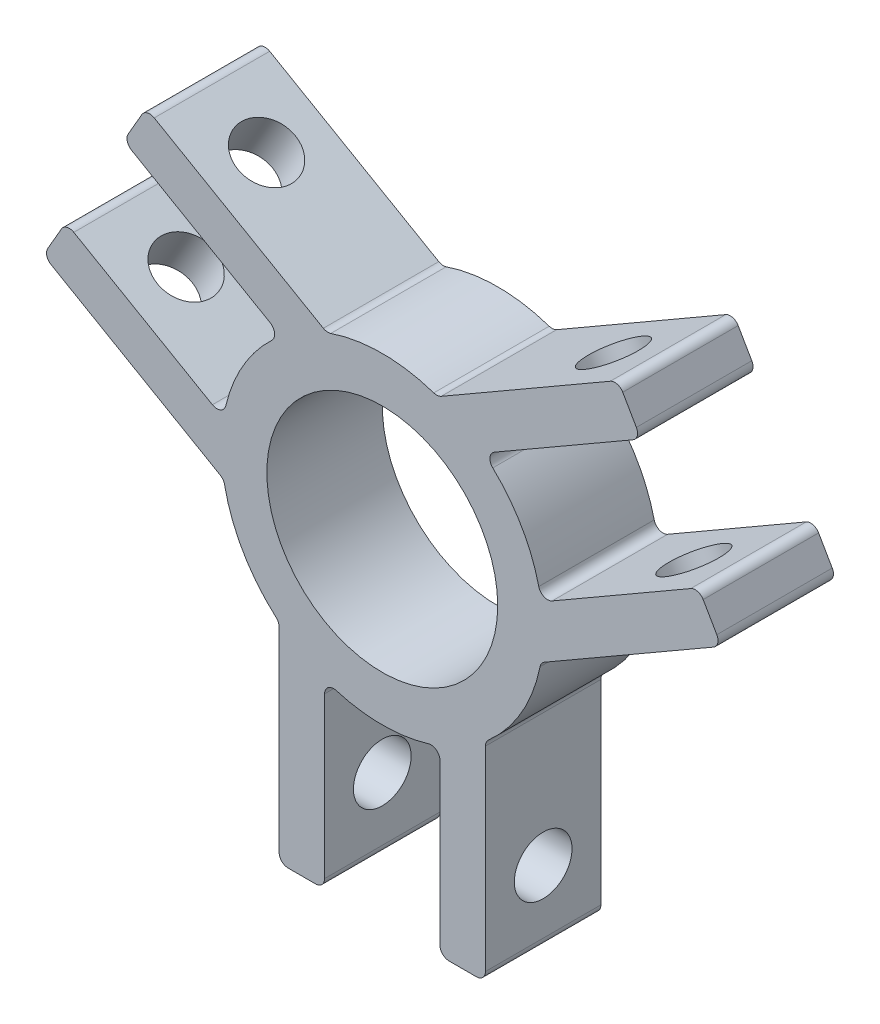
SolidWorks part; units mm, degrees
material "6061-T6 (SS)"
ref_plane "Plan de face" through (0, 0, 0) normal (0, 0, 1) x (1, 0, 0)
ref_plane "Plan de dessus" through (0, 0, 0) normal (0, 1, 0) x (1, 0, 0)
ref_plane "Plan de droite" through (0, 0, 0) normal (1, 0, 0) x (0, 0, -1)
sketch "Esquisse1" plane through (0, 0, 0) normal (0, 0, 1) x (1, 0, 0)
  line L0 (0, 0) -> (0, 50000) construction
  line L1 (0, 0) -> (-15.3286, -8.85) construction
  line L2 (0, 0) -> (15.3286, -8.85) construction
  circle A0 centre (0, 0) radius 17.7
  circle A1 centre (0, 0) radius 12.7
  dimension "D1" = 25.4
  dimension "D2" = 5
  dimension "D3" = 120
  dimension "D4" = 120
extrude "Boss.-Extru.1" add sketch "Esquisse1" along normal blind 12.7
sketch "Esquisse2" plane through (0, 0, 12.7) normal (0, 0, 1) x (1, 0, 0)
  line L0 (0, 0) -> (0, 50000) construction
  line L1 (0, 0) -> (-43301.2702, 25000) construction
  line L2 (0, 0) -> (43301.2702, 25000) construction
  line L3 (31.8812, 17.8236) -> (-24968.1188, 43319.0938) construction
  line L4 (28.4537, 23.7601) -> (11.1332, 13.7601)
  line L5 (28.4537, 23.7601) -> (25.9537, 28.0903)
  line L6 (25.9537, 28.0903) -> (6.0873, 16.6203)
  line L7 (11.1332, 13.7601) -> (6.0873, 16.6203)
  line L8 (17.4832, 2.7616) -> (17.4373, -3.0384)
  line L9 (37.3037, 8.4315) -> (17.4373, -3.0384)
  line L10 (34.8037, 12.7616) -> (37.3037, 8.4315)
  line L11 (34.8037, 12.7616) -> (17.4832, 2.7616)
  line L12 (11.35, -36.5217) -> (11.35, -13.5819)
  line L13 (6.35, -36.5217) -> (6.35, -16.5217)
  line L14 (6.35, -36.5217) -> (11.35, -36.5217)
  line L15 (6.35, -16.5217) -> (11.35, -13.5819)
  line L16 (-6.35, -16.5217) -> (-11.35, -13.5819)
  line L17 (-6.35, -36.5217) -> (-6.35, -16.5217)
  line L18 (-11.35, -36.5217) -> (-11.35, -13.5819)
  line L19 (-6.35, -36.5217) -> (-11.35, -36.5217)
  line L20 (-37.3037, 8.4315) -> (-17.4373, -3.0384)
  line L21 (-34.8037, 12.7616) -> (-17.4832, 2.7616)
  line L22 (-34.8037, 12.7616) -> (-37.3037, 8.4315)
  line L23 (-17.4832, 2.7616) -> (-17.4373, -3.0384)
  line L24 (-11.1332, 13.7601) -> (-6.0873, 16.6203)
  line L25 (-28.4537, 23.7601) -> (-11.1332, 13.7601)
  line L26 (-25.9537, 28.0903) -> (-6.0873, 16.6203)
  line L27 (-28.4537, 23.7601) -> (-25.9537, 28.0903)
  circle A0 centre (0, 0) radius 17.7 construction
  point P38 (0, 0)
  dimension "D1" = 60
  dimension "D2" = 60
  dimension "D3" = 6.35
  dimension "D4" = 5
  dimension "D5" = 20
  dimension "D6" = 3
extrude "Boss.-Extru.2" add sketch "Esquisse2" against normal up to surface (12.7 mm away) up to face at (12.7, 0, 0)
sketch "Esquisse3" plane through (5.675, 9.8294, 0) normal (0.5, 0.866, 0) x (0.866, -0.5, 0)
  line L0 (-36.5217, -6.35) -> (-13.5819, -6.35) construction
  line L1 (-36.5217, 0) -> (-36.5217, -12.7) construction
  line L2 (-13.5819, 0) -> (-13.5819, -12.7) construction
  circle A0 centre (-28.5842, -6.35) radius 3.175
  dimension "D1" = 6.35
  dimension "D2" = 7.9375
extrude "Enlèv. mat.-Extru.1" cut sketch "Esquisse3" against normal through all
sketch "Esquisse4" plane through (-5.675, 9.8294, 0) normal (-0.5, 0.866, 0) x (0.866, 0.5, 0)
  line L0 (36.5217, -6.35) -> (13.5819, -6.35) construction
  line L1 (36.5217, 0) -> (36.5217, -12.7) construction
  line L2 (13.5819, 0) -> (13.5819, -12.7) construction
  circle A0 centre (28.5842, -6.35) radius 3.175
  dimension "D1" = 6.35
  dimension "D2" = 7.9375
extrude "Enlèv. mat.-Extru.2" cut sketch "Esquisse4" against normal through all
sketch "Esquisse5" plane through (11.35, 0, 0) normal (1, 0, 0) x (0, 0, -1)
  line L0 (-6.35, -36.5217) -> (-6.35, -13.5819) construction
  line L1 (0, -36.5217) -> (-12.7, -36.5217) construction
  line L2 (0, -13.5819) -> (-12.7, -13.5819) construction
  circle A0 centre (-6.35, -28.5842) radius 3.175
  dimension "D2" = 6.35
  dimension "D1" = 7.9375
extrude "Enlèv. mat.-Extru.3" cut sketch "Esquisse5" against normal through all
fillet "Congé1" radius 1 24 edges at (-6.0873, 16.6203, 6.35) (6.0873, 16.6203, 6.35) (25.9537, 28.0903, 6.35) (28.4537, 23.7601, 6.35) (11.1332, 13.7601, 6.35) (17.4832, 2.7616, 6.35) (34.8037, 12.7616, 6.35) (37.3037, 8.4315, 6.35) (17.4373, -3.0384, 6.35) (11.35, -13.5819, 6.35) (11.35, -36.5217, 6.35) (6.35, -36.5217, 6.35) (6.35, -16.5217, 6.35) (-6.35, -16.5217, 6.35) (-6.35, -36.5217, 6.35) (-11.35, -36.5217, 6.35) (-11.35, -13.5819, 6.35) (-17.4373, -3.0384, 6.35) (-37.3037, 8.4315, 6.35) (-34.8037, 12.7616, 6.35) (-28.4537, 23.7601, 6.35) (-25.9537, 28.0903, 6.35) (-17.4832, 2.7616, 6.35) (-11.1332, 13.7601, 6.35)
